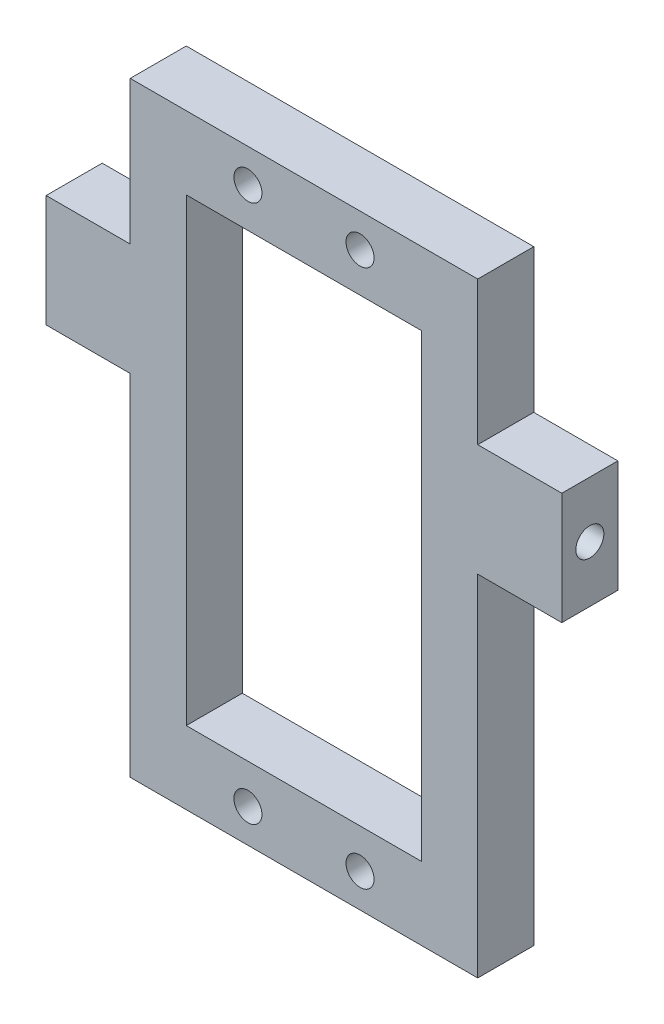
SolidWorks part; units mm, degrees
ref_plane "前视基准面" through (0, 0, 0) normal (0, 0, 1) x (1, 0, 0)
ref_plane "上视基准面" through (0, 0, 0) normal (0, 1, 0) x (1, 0, 0)
ref_plane "右视基准面" through (0, 0, 0) normal (1, 0, 0) x (0, 0, -1)
sketch "草图1" plane through (0, 0, 0) normal (0, 0, 1) x (1, 0, 0)
  line L1 (10.5, -20.5) -> (-10.5, -20.5)
  line L2 (10.5, -20.5) -> (10.5, 20.5)
  line L3 (10.5, 20.5) -> (-10.5, 20.5)
  line L4 (-10.5, -20.5) -> (-10.5, 20.5)
  line L5 (10.5, -20.5) -> (-10.5, 20.5) construction
  line L6 (10.5, 20.5) -> (-10.5, -20.5) construction
  line L7 (15.5, -27) -> (-15.5, -27)
  line L8 (15.5, -27) -> (15.5, 27)
  line L9 (15.5, 27) -> (-15.5, 27)
  line L10 (-15.5, -27) -> (-15.5, 27)
  line L11 (15.5, -27) -> (-15.5, 27) construction
  line L12 (15.5, 27) -> (-15.5, -27) construction
  point P0 (0, 0)
  point P6 (0, 0)
  dimension "D1" = 21
  dimension "D2" = 41
  dimension "D3" = 6.5
  dimension "D4" = 5
extrude "凸台-拉伸1" add sketch "草图1" along normal blind 5
sketch "草图2" plane through (15.5, 0, 0) normal (1, 0, 0) x (0, 0, -1)
  line L0 (-5, 4.2) -> (0, 4.2)
  line L1 (-5, -27) -> (-5, 27) construction
  line L2 (0, 4.2) -> (0, 14.2)
  line L3 (0, -27) -> (0, 27) construction
  line L4 (0, 14.2) -> (-5, 14.2)
  line L5 (-5, 14.2) -> (-5, 4.2)
  line L6 (-5, -27) -> (0, -27) construction
  dimension "D1" = 31.2
  dimension "D2" = 10
extrude "凸台-拉伸2" add sketch "草图2" along normal blind 7.5
mirror "镜向1" about plane through (0, 0, 0) normal (1, 0, 0) of "凸台-拉伸2"
hole_wizard "M3 螺纹孔1" positions "草图3" profile "草图4" tap size "M3" standard "GB" end condition through all
sketch "草图3" plane through (0, 0, 0) normal (0, 0, -1) x (-1, 0, 0)
  point P0 (-5, -24)
  point P3 (5, -24)
  point P6 (-5, 24)
  point P9 (5, 24)
sketch "草图4" plane through (5, -24, 0) normal (1, 0, 0) x (0, 1, 0)
  line L0 (0, 0) -> (0, 5)
  line L1 (0, 5) -> (1.25, 5)
  line L2 (1.25, 5) -> (1.25, 0)
  line L5 (1.25, 0) -> (0, 0)
  line L11 (0, -6.35) -> (0, 107.95) construction
  dimension "通孔螺纹孔钻头直径" = 2.5
  dimension "通孔螺纹孔钻头深度" = 5
cosmetic thread "孔螺蚊线1" parameters "D2"=3
cosmetic thread "孔螺蚊线2" parameters "D2"=3
cosmetic thread "孔螺蚊线3" parameters "D2"=3
cosmetic thread "孔螺蚊线4" parameters "D2"=3
hole_wizard "M3 螺纹孔2" positions "草图5" profile "草图7" tap size "M3" standard "GB"
sketch "草图5" plane through (23, 0, 0) normal (1, 0, 0) x (0, 0, -1)
  line L0 (-5, 9.2) -> (0, 9.2) construction
  line L1 (-5, 14.2) -> (-5, 4.2) construction
  line L2 (0, 4.2) -> (0, 14.2) construction
  point P0 (-2.5, 9.2)
sketch "草图7" plane through (23, 9.2, 2.5) normal (0, 1, 0) x (0, 0, -1)
  line L0 (0, 0) -> (0, 6.2511)
  line L1 (0, 6.2511) -> (1.25, 5.5)
  line L2 (1.25, 5.5) -> (1.25, 0)
  line L5 (1.25, 0) -> (0, 0)
  line L10 (0, 6.2511) -> (-1.25, 5.5) construction
  line L11 (0, -6.35) -> (0, 107.95) construction
  dimension "螺纹孔钻头直径" = 2.5
  dimension "螺纹孔钻头深度" = 5.5
  dimension "导头角度" = 118
cosmetic thread "孔螺蚊线5" parameters "D1"=4, "D2"=3
mirror "镜向2" about plane through (0, 0, 0) normal (1, 0, 0) of "M3 螺纹孔2"
